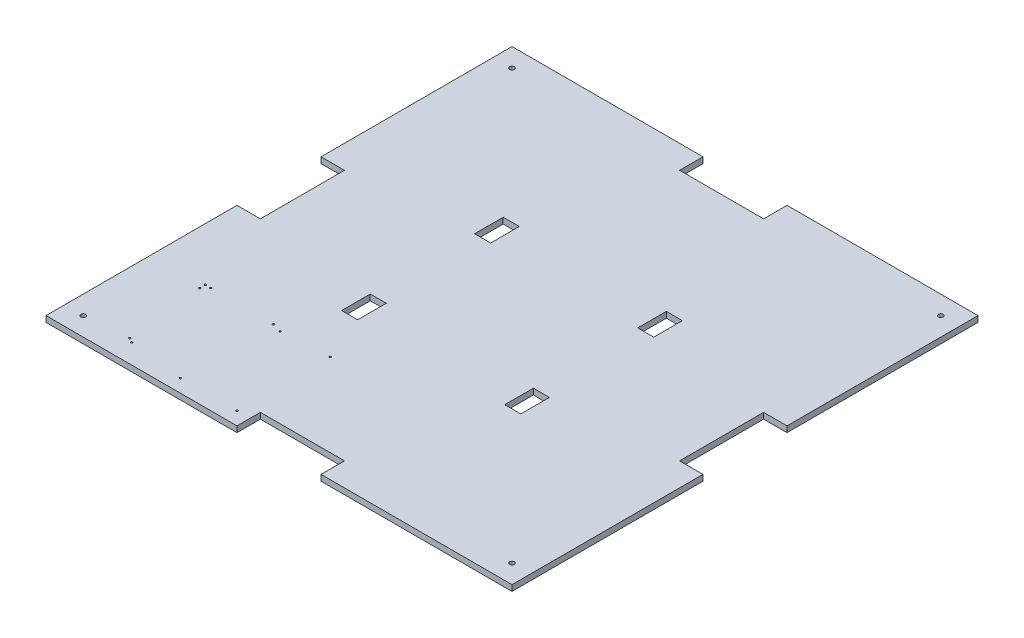
SolidWorks part; units mm, degrees
ref_plane "Front Plane" through (0, 0, 0) normal (0, 0, 1) x (1, 0, 0)
ref_plane "Top Plane" through (0, 0, 0) normal (0, 1, 0) x (1, 0, 0)
ref_plane "Right Plane" through (0, 0, 0) normal (1, 0, 0) x (0, 0, -1)
sketch "Sketch2" plane through (0, 0, 0) normal (0, 1, 0) x (1, 0, 0)
  line L1 (-125, -125) -> (125, -125)
  line L2 (-125, -125) -> (-125, 125)
  line L3 (-125, 125) -> (125, 125)
  line L4 (125, -125) -> (125, 125)
  line L5 (-125, -125) -> (125, 125) construction
  line L6 (-125, 125) -> (125, -125) construction
  point P0 (0, 0)
  dimension "D1" = 250
  dimension "D2" = 250
extrude "Boss-Extrude1" add sketch "Sketch2" along normal blind 3.175
sketch "Sketch3" plane through (0, 3.175, 0) normal (0, 1, 0) x (1, 0, 0)
  line L0 (-125, 0) -> (125, 0) construction
  line L1 (-125, 125) -> (-125, -125) construction
  line L2 (125, -125) -> (125, 125) construction
  line L3 (-43.75, 125) -> (-43.75, -125) construction
  line L4 (125, 125) -> (-125, 125) construction
  line L5 (-125, -125) -> (125, -125) construction
  line L6 (0, 125) -> (0, -125) construction
  line L11 (-48.05, 28) -> (-39.45, 28)
  line L12 (-48.05, 28) -> (-48.05, 43.35)
  line L13 (-48.05, 43.35) -> (-39.45, 43.35)
  line L14 (-39.45, 28) -> (-39.45, 43.35)
  line L15 (-48.05, 28) -> (-39.45, 43.35) construction
  line L16 (-48.05, 43.35) -> (-39.45, 28) construction
  line L21 (-48.05, -43.35) -> (-39.45, -43.35)
  line L22 (-48.05, -43.35) -> (-48.05, -28)
  line L23 (-48.05, -28) -> (-39.45, -28)
  line L24 (-39.45, -43.35) -> (-39.45, -28)
  line L25 (-48.05, -43.35) -> (-39.45, -28) construction
  line L26 (-48.05, -28) -> (-39.45, -43.35) construction
  line L27 (48.05, -28) -> (39.45, -28)
  line L28 (39.45, -43.35) -> (39.45, -28)
  line L29 (48.05, -43.35) -> (39.45, -43.35)
  line L30 (48.05, -43.35) -> (48.05, -28)
  line L31 (48.05, 43.35) -> (39.45, 43.35)
  line L32 (39.45, 28) -> (39.45, 43.35)
  line L33 (48.05, 28) -> (39.45, 28)
  line L34 (48.05, 28) -> (48.05, 43.35)
  point P12 (-43.75, 35.675)
  point P17 (-43.75, -35.675)
  dimension "D1" = 43.75
  dimension "D2" = 8.6
  dimension "D3" = 15.35
  dimension "D4" = 56
  dimension "D5" = 28
extrude "Cut-Extrude1" cut sketch "Sketch3" against normal blind 10
sketch "Sketch4" plane through (0, 3.175, 0) normal (0, 1, 0) x (1, 0, 0)
  line L0 (0, 125) -> (0, -125) construction
  line L1 (125, 125) -> (-125, 125) construction
  line L2 (-125, -125) -> (125, -125) construction
  line L3 (-125, 0) -> (125, 0) construction
  line L4 (-125, 125) -> (-125, -125) construction
  line L5 (125, -125) -> (125, 125) construction
  line L7 (-22.55, 137.55) -> (22.55, 137.55)
  line L8 (-22.55, 137.55) -> (-22.55, 112.45)
  line L9 (-22.55, 112.45) -> (22.55, 112.45)
  line L10 (22.55, 137.55) -> (22.55, 112.45)
  line L11 (-22.55, 137.55) -> (22.55, 112.45) construction
  line L12 (-22.55, 112.45) -> (22.55, 137.55) construction
  line L28 (137.55, 22.55) -> (112.45, 22.55)
  line L29 (137.55, 22.55) -> (137.55, -22.55)
  line L30 (137.55, -22.55) -> (112.45, -22.55)
  line L31 (112.45, 22.55) -> (112.45, -22.55)
  line L32 (22.55, -137.55) -> (22.55, -112.45)
  line L33 (22.55, -137.55) -> (-22.55, -137.55)
  line L34 (-22.55, -137.55) -> (-22.55, -112.45)
  line L35 (22.55, -112.45) -> (-22.55, -112.45)
  line L36 (-137.55, -22.55) -> (-112.45, -22.55)
  line L37 (-137.55, -22.55) -> (-137.55, 22.55)
  line L38 (-137.55, 22.55) -> (-112.45, 22.55)
  line L39 (-112.45, -22.55) -> (-112.45, 22.55)
  point P31 (-25, 25)
  point P32 (0, 0)
  dimension "D1" = 25.1
  dimension "D2" = 45.1
  dimension "D3" = 4
extrude "Cut-Extrude2" cut sketch "Sketch4" against normal blind 10
hole_wizard "M3 Tapped Hole1" positions "Sketch5" profile "Sketch6" tap size "M3" standard "ISO" end condition through all
sketch "Sketch5" plane through (0, 3.175, 0) normal (0, 1, 0) x (1, 0, 0)
  line L0 (-22.55, 125) -> (-125, 125) construction
  line L1 (-125, 125) -> (-125, 22.55) construction
  point P0 (-115, 115)
  dimension "D1" = 10
  dimension "D2" = 10
sketch "Sketch6" plane through (-115, 3.175, -115) normal (1, 0, 0) x (0, 0, 1)
  line L0 (0, 0) -> (0, 3.175)
  line L1 (0, 3.175) -> (1.25, 3.175)
  line L2 (1.25, 3.175) -> (1.25, 0)
  line L5 (1.25, 0) -> (0, 0)
  line L11 (0, -6.35) -> (0, 107.95) construction
  dimension "Thru Tap Drill Dia." = 2.5
  dimension "Thru Tap Drill Depth" = 3.175
cosmetic thread "Hole Thread1" parameters "D2"=3
hole_wizard "M3 Tapped Hole2" positions "Sketch7" profile "Sketch8" tap size "M3" standard "ISO" end condition through all
sketch "Sketch7" plane through (0, 3.175, 0) normal (0, 1, 0) x (1, 0, 0)
  line L0 (-125, -125) -> (-22.55, -125) construction
  line L1 (-125, -22.55) -> (-125, -125) construction
  line L2 (125, -125) -> (125, -22.55) construction
  line L3 (22.55, -125) -> (125, -125) construction
  line L4 (125, 22.55) -> (125, 125) construction
  line L5 (125, 125) -> (22.55, 125) construction
  point P0 (115, 115)
  point P2 (115, -115)
  point P4 (-115, -115)
  dimension "D1" = 10
  dimension "D2" = 10
  dimension "D3" = 10
  dimension "D4" = 10
  dimension "D5" = 10
  dimension "D6" = 10
sketch "Sketch8" plane through (115, 3.175, -115) normal (1, 0, 0) x (0, 0, 1)
  line L0 (0, 0) -> (0, 3.175)
  line L1 (0, 3.175) -> (1.25, 3.175)
  line L2 (1.25, 3.175) -> (1.25, 0)
  line L5 (1.25, 0) -> (0, 0)
  line L11 (0, -6.35) -> (0, 107.95) construction
  dimension "Thru Tap Drill Dia." = 2.5
  dimension "Thru Tap Drill Depth" = 3.175
cosmetic thread "Hole Thread2" parameters "D2"=3
cosmetic thread "Hole Thread3" parameters "D2"=3
cosmetic thread "Hole Thread4" parameters "D2"=3
sketch "Sketch9" plane through (0, 3.175, 0) normal (0, 1, 0) x (1, 0, 0)
  circle A0 centre (-92.05, -113) radius 0.5
  circle A1 centre (-89.55, -114.5) radius 0.5
  circle A2 centre (-59.95, -118) radius 0.5
  circle A3 centre (-29.55, -118) radius 0.5
  circle A4 centre (-29.55, -68) radius 0.5
  circle A5 centre (-54.85, -69.6) radius 0.5
  circle A6 centre (-59.95, -68) radius 0.5
  circle A7 centre (-96.55, -68) radius 0.5
  circle A8 centre (-93.65, -68) radius 0.5
  circle A9 centre (-96.55, -71) radius 0.5
extrude "Cut-Extrude3" cut sketch "Sketch9" against normal through all
